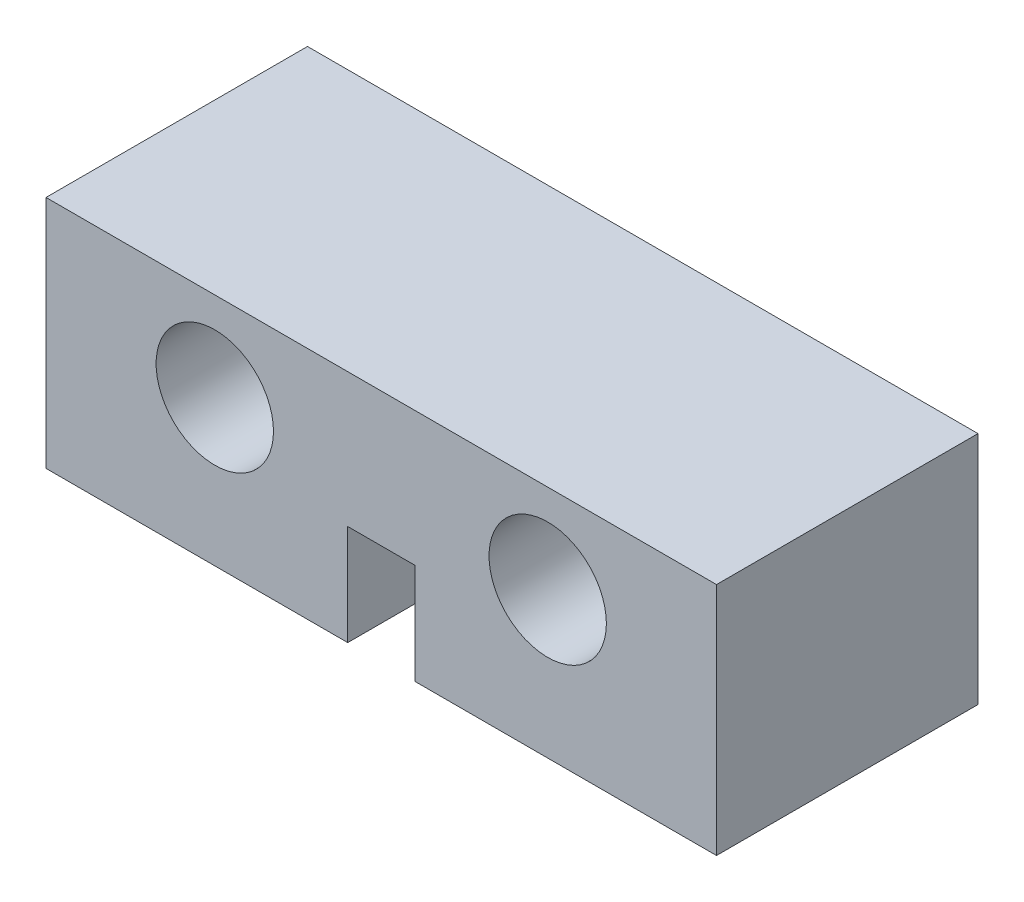
SolidWorks part; units mm, degrees
ref_plane "前视基准面" through (0, 0, 0) normal (0, 0, 1) x (1, 0, 0)
ref_plane "上视基准面" through (0, 0, 0) normal (0, 1, 0) x (1, 0, 0)
ref_plane "右视基准面" through (0, 0, 0) normal (1, 0, 0) x (0, 0, -1)
sketch "草图1" plane through (0, 0, 0) normal (0, 0, 1) x (1, 0, 0)
  line L1 (-10, -3.5) -> (10, -3.5)
  line L2 (-10, -3.5) -> (-10, 3.5)
  line L3 (-10, 3.5) -> (10, 3.5)
  line L4 (10, -3.5) -> (10, 3.5)
  line L5 (-10, -3.5) -> (10, 3.5) construction
  line L6 (-10, 3.5) -> (10, -3.5) construction
  point P0 (0, 0)
  dimension "D1" = 20
  dimension "D2" = 7
extrude "凸台-拉伸1" add sketch "草图1" along normal blind 7.8
sketch "草图2" plane through (0, 0, 7.8) normal (0, 0, 1) x (1, 0, 0)
  line L0 (0, 0) -> (0, 6.0817) construction
  line L1 (-10, -3.5) -> (10, -3.5) construction
  circle A0 centre (-4.965, 0.85) radius 1.75
  circle A1 centre (4.965, 0.85) radius 1.75
  point P7 (0, 0)
  dimension "D1" = 3.5
  dimension "D2" = 3.5
  dimension "D3" = 4.35
  dimension "D4" = 9.93
extrude "切除-拉伸1" cut sketch "草图2" against normal blind 7.8
sketch "草图3" plane through (0, 0, 7.8) normal (0, 0, 1) x (1, 0, 0)
  line L0 (-10, -3.5) -> (10, -3.5) construction
  line L1 (-1, -3.5) -> (1, -3.5)
  line L2 (-1, -3.5) -> (-1, -0.5)
  line L3 (-1, -0.5) -> (1, -0.5)
  line L4 (1, -3.5) -> (1, -0.5)
  line L5 (0, 0) -> (0, -6.8607) construction
  dimension "D1" = 3
  dimension "D2" = 2
extrude "切除-拉伸2" cut sketch "草图3" against normal blind 7.8
